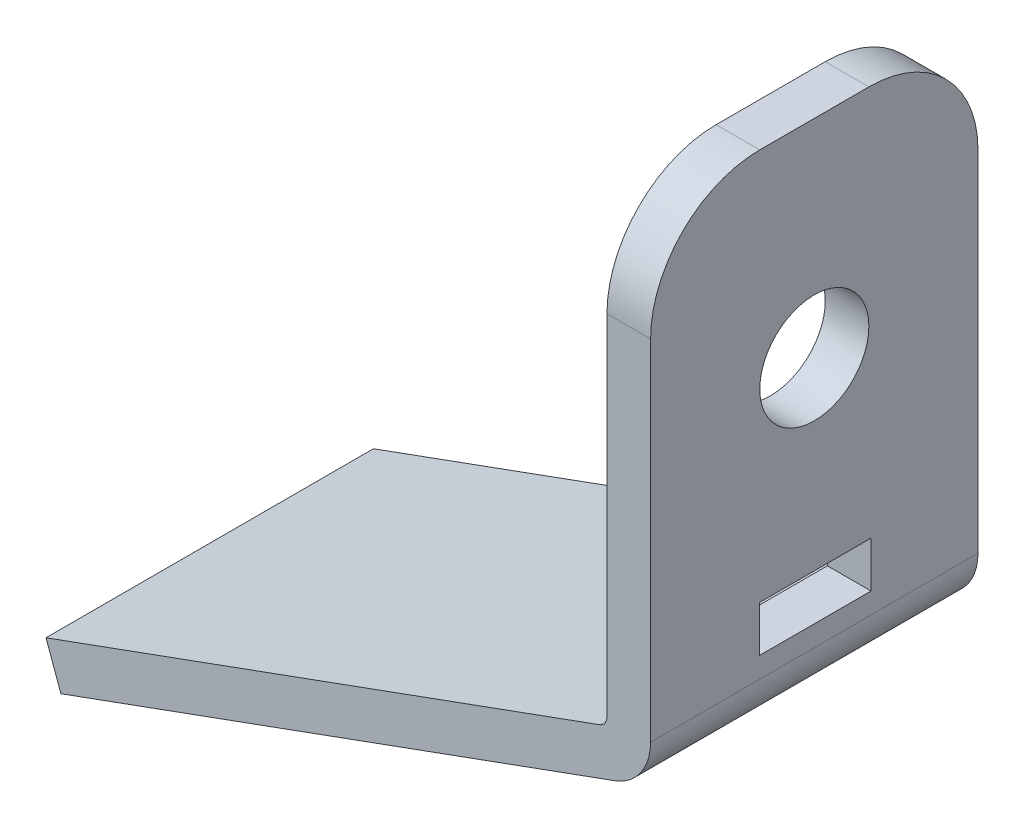
SolidWorks part; units mm, degrees
material "Stal węglowa"
ref_plane "Płaszczyzna przednia" through (0, 0, 0) normal (0, 0, 1) x (1, 0, 0)
ref_plane "Płaszczyzna górna" through (0, 0, 0) normal (0, 1, 0) x (1, 0, 0)
ref_plane "Płaszczyzna prawa" through (0, 0, 0) normal (1, 0, 0) x (0, 0, -1)
sketch "Szkic1" plane through (0, 0, 0) normal (0, 0, 1) x (1, 0, 0)
  line L0 (2, -360.3201) -> (2, -355.3201) construction
  line L1 (2, -355.3201) -> (0, -355.3201) construction
  line L2 (0, -355.3201) -> (0, -360.3201) construction
  line L6 (0.3551, -378.6722) -> (-25.0167, -387.9068)
  line L7 (-25.0167, -387.9068) -> (-25.7007, -386.0274)
  line L8 (2, -376.323) -> (2, -375.3201) construction
  line L18 (2, -375.3201) -> (2, -360.3201) construction
  line L19 (0, -360.3201) -> (0, -373.3248) construction
  line L21 (2, -360.3201) -> (2, -355.3201)
  line L22 (2, -355.3201) -> (0, -355.3201)
  line L23 (0, -355.3201) -> (0, -360.3201)
  line L29 (2, -376.323) -> (2, -375.3201)
  line L39 (2, -375.3201) -> (2, -360.3201)
  line L40 (0, -360.3201) -> (0, -373.3248)
  line L42 (0, -373.3248) -> (0, -375.3201)
  line L46 (0, -375.3201) -> (0, -376.323)
  line L47 (-0.329, -376.7928) -> (-25.7007, -386.0274)
  arc A0 (0.3551, -378.6722) -> (2, -376.323) centre (-0.5, -376.323) ccw construction
  arc A4 (0.3551, -378.6722) -> (2, -376.323) centre (-0.5, -376.323) ccw
  arc A8 (0, -376.323) -> (-0.329, -376.7928) centre (-0.5, -376.323) cw
extrude "Dodanie-wyciągnięcie1" add sketch "Szkic1" against normal blind 15
sketch "Szkic2" plane through (2, 0, 0) normal (1, 0, 0) x (0, 0, -1)
  circle A1 centre (7.5, -364.8201) radius 2.5
extrude "Wytnij-wyciągnięcie3" cut sketch "Szkic2" against normal blind 15
sketch "Szkic4" plane through (2, 0, 0) normal (1, 0, 0) x (0, 0, -1)
  line L0 (5, -373.273) -> (5, -375.373)
  line L1 (10.1, -375.373) -> (5, -375.373)
  line L3 (10.1, -375.373) -> (10.1, -373.273)
  line L4 (10.1, -373.273) -> (5, -373.273)
extrude "Wytnij-wyciągnięcie8" cut sketch "Szkic4" against normal blind 15
fillet "Zaokrąglenie1" radius 5 2 edges at (1, -355.3201, 0) (1, -355.3201, -15)
